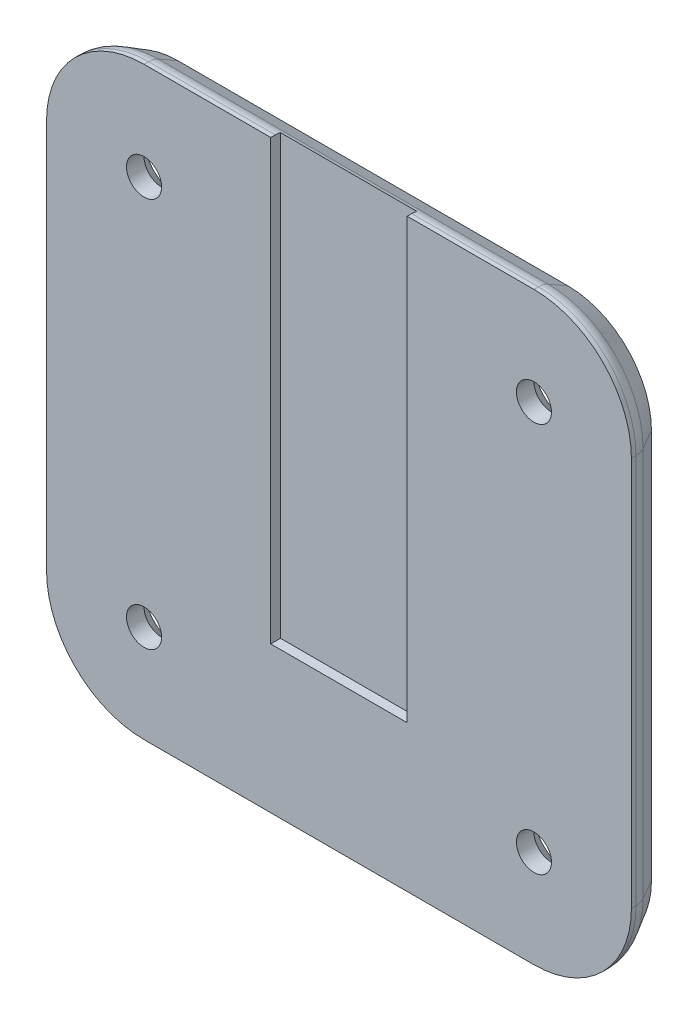
SolidWorks part; units mm, degrees
ref_plane "Front Plane" through (0, 0, 0) normal (0, 0, 1) x (1, 0, 0)
ref_plane "Top Plane" through (0, 0, 0) normal (0, 1, 0) x (1, 0, 0)
ref_plane "Right Plane" through (0, 0, 0) normal (1, 0, 0) x (0, 0, -1)
sketch "Sketch1" plane through (0, 0, 0) normal (0, 0, 1) x (1, 0, 0)
  line L1 (-20, 30) -> (20, 30)
  line L2 (-30, 20) -> (-30, -20)
  line L3 (-20, -30) -> (20, -30)
  line L4 (30, 20) -> (30, -20)
  arc A0 (20, 30) -> (30, 20) centre (20, 20) cw
  arc A1 (20, -30) -> (30, -20) centre (20, -20) ccw
  arc A2 (-30, -20) -> (-20, -30) centre (-20, -20) ccw
  arc A3 (-20, 30) -> (-30, 20) centre (-20, 20) ccw
  point P4 (0, 30)
  point P7 (-30, 0)
  point P9 (30, 30)
  point P14 (-30, -30)
  point P17 (-30, 30)
  dimension "D3" = 10
  dimension "D1" = 60
  dimension "D2" = 60
extrude "Boss-Extrude1" add sketch "Sketch1" along normal blind 3.5
hole_wizard "CSK for M3 Countersunk Flat Head Screw1" positions "Sketch2" profile "Sketch3" countersink size "M3" standard "DIN" end condition through all
sketch "Sketch2" plane through (0, 0, 3.5) normal (0, 0, 1) x (1, 0, 0)
  line L7 (20, 20) -> (20, -20) construction
  line L9 (20, 20) -> (-20, 20) construction
  point P0 (-20, 20)
  point P2 (20, 20)
  point P4 (20, -20)
  point P6 (-20, -20)
  point P39 (0, 20)
  point P41 (20, 0)
  dimension "D1" = 40
  dimension "D2" = 40
sketch "Sketch3" plane through (-20, 20, 3.5) normal (1, 0, 0) x (0, -1, 0)
  line L0 (0, 0) -> (0, 3.5)
  line L1 (0, 3.5) -> (1.8, 3.5)
  line L2 (1.8, 3.5) -> (1.8, 1.7)
  line L3 (1.8, 1.7) -> (3.5, 0)
  line L5 (3.5, 0) -> (0, 0)
  line L6 (-1.8, 1.7) -> (-3.5, 0) construction
  line L11 (0, -6.35) -> (0, 107.95) construction
  dimension "Thru Hole Dia." = 3.6
  dimension "Thru Hole Depth" = 3.5
  dimension "Near C'Sink Dia." = 7
  dimension "Near C'Sink Angle" = 90
chamfer "Chamfer1" distance 2.5 angle 30 8 edges at (0, -30, 3.5) (27.0711, -27.0711, 3.5) (-27.0711, -27.0711, 3.5) (30, 0, 3.5) (-30, 0, 3.5) (27.0711, 27.0711, 3.5) (-27.0711, 27.0711, 3.5) (0, 30, 3.5)
fillet "Fillet2" radius 2 8 edges at (-27.0711, 27.0711, 1) (-30, 0, 1) (-27.0711, -27.0711, 1) (0, -30, 1) (27.0711, -27.0711, 1) (30, 0, 1) (27.0711, 27.0711, 1) (0, 30, 1)
sketch "Sketch4" plane through (0, 0, 0) normal (0, 1, 0) x (1, 0, 0)
  line L0 (20, 0) -> (-20, 0) construction
  line L1 (-7, 3.1158) -> (7, 3.1158)
  line L2 (-7, 3.1158) -> (-7, -1)
  line L3 (-7, -1) -> (7, -1)
  line L4 (7, 3.1158) -> (7, -1)
  point P6 (0, -1)
  dimension "D1" = 14
  dimension "D2" = 1
extrude "Cut-Extrude1" cut sketch "Sketch4" against normal blind 15 and the other way through all
move or copy body "Body-Move/Copy1" bodies to move or copy 103 copy no rotation origin (0, 0, 1.75) rotation axis (0, 1, 0) rotation angle 180
